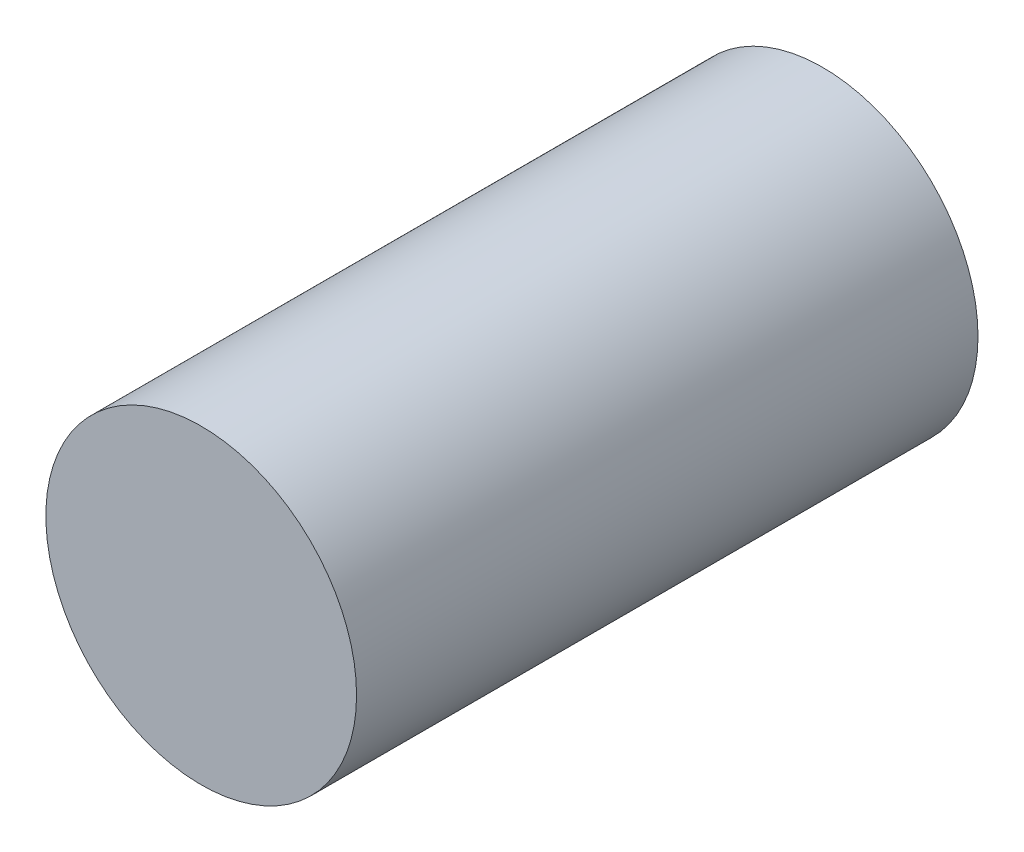
SolidWorks part; units mm, degrees
material "Aluminum Bronze"
ref_plane "Front Plane" through (0, 0, 0) normal (0, 0, 1) x (1, 0, 0)
ref_plane "Top Plane" through (0, 0, 0) normal (0, 1, 0) x (1, 0, 0)
ref_plane "Right Plane" through (0, 0, 0) normal (1, 0, 0) x (0, 0, -1)
sketch "Sketch1" plane through (0, 0, 0) normal (0, 0, 1) x (1, 0, 0)
  circle A0 centre (0, 0) radius 5
  dimension "D1" = 10
extrude "Boss-Extrude1" add sketch "Sketch1" along normal mid plane 20
